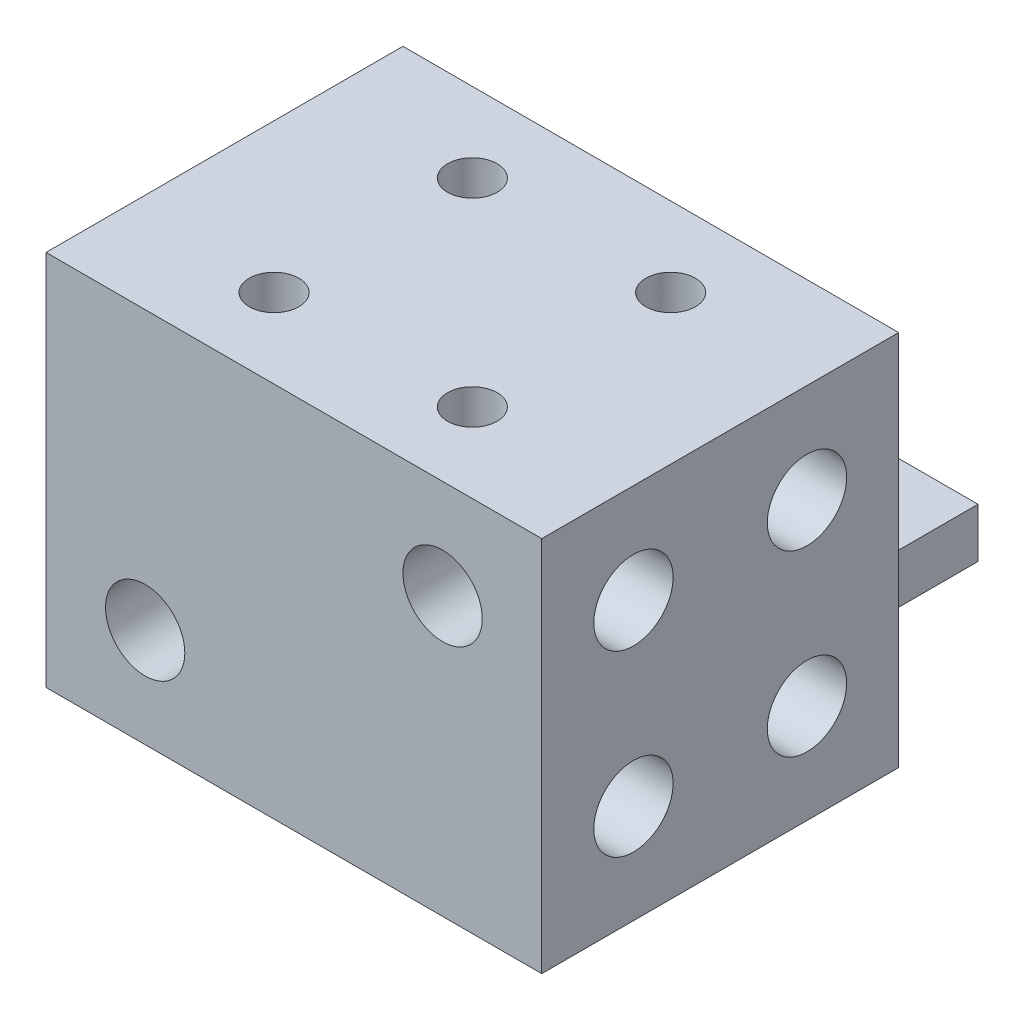
SolidWorks part; units mm, degrees
ref_plane "Front Plane" through (0, 0, 0) normal (0, 0, 1) x (1, 0, 0)
ref_plane "Top Plane" through (0, 0, 0) normal (0, 1, 0) x (1, 0, 0)
ref_plane "Right Plane" through (0, 0, 0) normal (1, 0, 0) x (0, 0, -1)
sketch "Sketch2" plane through (0, 0, 0) normal (0, 1, 0) x (1, 0, 0)
  line L1 (25, -18) -> (-25, -18)
  line L2 (25, -18) -> (25, 18)
  line L3 (25, 18) -> (-25, 18)
  line L4 (-25, -18) -> (-25, 18)
  line L5 (25, -18) -> (-25, 18) construction
  line L6 (25, 18) -> (-25, -18) construction
  point P0 (0, 0)
  dimension "D1" = 50
  dimension "D2" = 36
extrude "Boss-Extrude1" add sketch "Sketch2" along normal mid plane 38
sketch "Sketch3" plane through (0, -19, 0) normal (0, -1, 0) x (1, 0, 0)
  line L0 (25, -18) -> (-25, -18) construction
  line L1 (-11, 4) -> (11, 4)
  line L2 (-11, 4) -> (-11, -40)
  line L3 (-11, -40) -> (11, -40)
  line L4 (11, 4) -> (11, -40)
  line L5 (-11, 4) -> (11, -40) construction
  line L6 (-11, -40) -> (11, 4) construction
  point P0 (0, -18)
  dimension "D1" = 22
  dimension "D2" = 22
extrude "Boss-Extrude3" add sketch "Sketch3" against normal blind 5
sketch "Sketch4" plane through (-25, 0, 0) normal (-1, 0, 0) x (0, 0, 1)
  line L0 (-18, -19) -> (18, -19) construction
  line L3 (27.5, 0) -> (-27.5, 0) construction
  line L4 (0, -20.9) -> (0, 20.9) construction
  circle A7 centre (-8.75, -9) radius 4
  circle A8 centre (8.75, -9) radius 4
  circle A9 centre (8.75, 9) radius 4
  circle A10 centre (-8.75, 9) radius 4
  dimension "D2" = 8
  dimension "D1" = 17.5
  dimension "D3" = 10
extrude "Cut-Extrude1" cut sketch "Sketch4" along direction (-1, 0, 0) on the side against the normal up to surface (50 mm away)
sketch "Sketch5" plane through (0, 0, -18) normal (0, 0, -1) x (-1, 0, 0)
  line L2 (0, 20.9) -> (0, -20.9) construction
  line L3 (-25, -19) -> (-11, -19) construction
  line L4 (-25, 19) -> (25, 19) construction
  circle A0 centre (-15, -9) radius 4
  circle A2 centre (15, 9) radius 4
  dimension "D4" = 8
  dimension "D5" = 8
  dimension "D1" = 10
  dimension "D2" = 15
  dimension "D3" = 15
  dimension "D6" = 10
extrude "Cut-Extrude2" cut sketch "Sketch5" against normal blind 15
sketch "Sketch6" plane through (0, 0, 18) normal (0, 0, 1) x (1, 0, 0)
  line L0 (-25, -19) -> (25, -19) construction
  line L2 (0, -20.9) -> (0, 20.9) construction
  line L4 (-25, 19) -> (25, 19) construction
  circle A0 centre (-15, -9) radius 4
  circle A1 centre (15, 9) radius 4
  dimension "D6" = 8
  dimension "D7" = 8
  dimension "D1" = 10
  dimension "D2" = 10
  dimension "D3" = 15
  dimension "D5" = 15
extrude "Cut-Extrude3" cut sketch "Sketch6" against normal blind 16
sketch "Sketch24" plane through (0, -14, 0) normal (0, 1, 0) x (1, 0, 0)
  line L0 (0, -19.25) -> (0, 19.25) construction
  line L1 (-11, 40) -> (11, 40) construction
  circle A0 centre (0, 29) radius 7.5
  dimension "D1" = 15
  dimension "D2" = 11
extrude "Cut-Extrude4" cut sketch "Sketch24" against normal up to surface (5 mm away) up to face at (0, -19, -14.5)
ref_plane "Plane1" through (0, -16, 0) normal (0, -1, 0) x (-1, 0, 0)
sketch "Sketch25" plane through (0, -19, 0) normal (0, 1, 0) x (1, 0, 0)
  line L0 (0, 28.103) -> (0, -26.1082) construction
  line L1 (-22.5, 13.5) -> (22.5, 13.5) construction
  line L2 (-22.5, 13.5) -> (-22.5, -13.5) construction
  line L3 (-22.5, -13.5) -> (22.5, -13.5) construction
  line L4 (22.5, 13.5) -> (22.5, -13.5) construction
  line L6 (-20.9, 0) -> (20.9, 0) construction
  line L7 (-32.0325, 0) -> (39.5984, 0) construction
  line L8 (0, -20.9) -> (0, 20.9) construction
  circle A0 centre (-10, 10) radius 1.5
  circle A1 centre (10, 10) radius 1.5
  circle A2 centre (10, -10) radius 1.5
  circle A3 centre (-10, -10) radius 1.5
  point P0 (0, 0)
  point P22 (0, 0)
  dimension "D5" = 3
  dimension "D1" = 45
  dimension "D2" = 27
  dimension "D3" = 20
  dimension "D4" = 20
extrude "Cut-Extrude5" cut sketch "Sketch25" along normal up to surface (3 mm away)
sketch "Sketch26" plane through (0, -16, 0) normal (0, -1, 0) x (-1, 0, 0)
  circle A0 centre (-10, 10) radius 2.5
  circle A1 centre (10, 10) radius 2.5
  circle A2 centre (10, -10) radius 2.5
  circle A3 centre (-10, -10) radius 2.5
  dimension "D1" = 5
extrude "Cut-Extrude6" cut sketch "Sketch26" against normal through all
